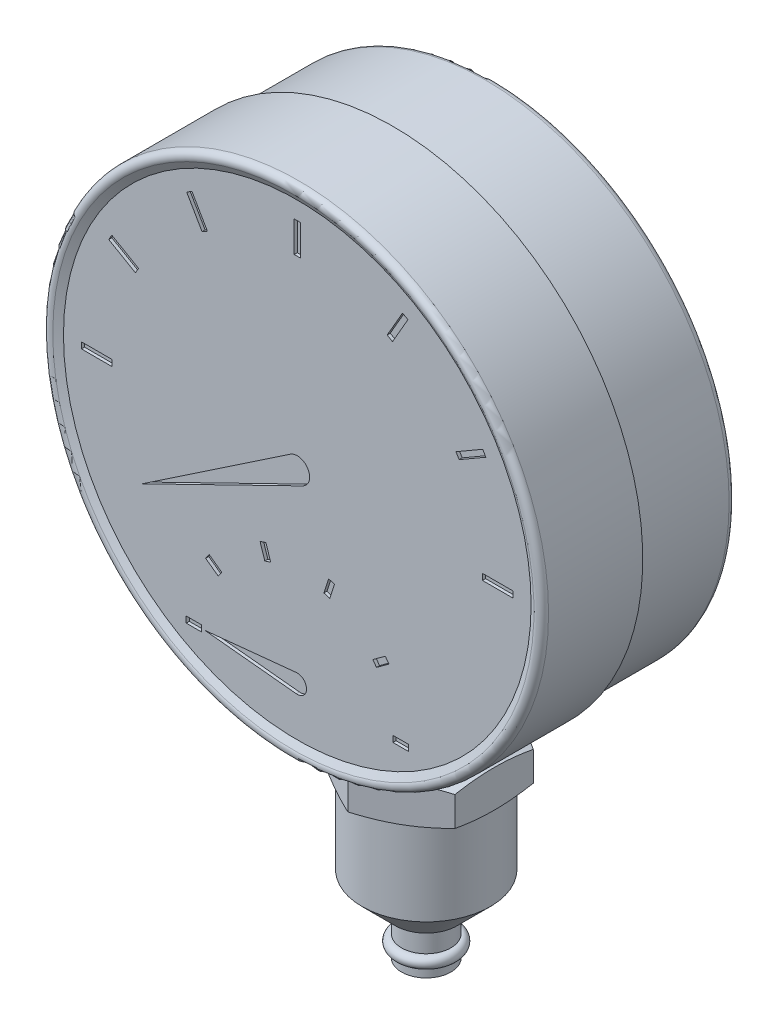
SolidWorks part; units mm, degrees
ref_plane "Horní" through (0, 0, 0) normal (0, 0, 1) x (1, 0, 0)
ref_plane "Přední" through (0, 0, 0) normal (0, 1, 0) x (1, 0, 0)
ref_plane "Pravá" through (0, 0, 0) normal (1, 0, 0) x (0, 0, -1)
sketch "Skica1" plane through (0, 0, 0) normal (1, 0, 0) x (0, 0, -1)
  line L0 (0, 40.5) -> (1.5, 37.9019)
  line L1 (0, 40.5) -> (17, 40.5)
  line L2 (1.5, 0) -> (33, 0)
  line L4 (33, 39.5) -> (33, 0)
  line L8 (0, 0) -> (-34.5616, 0) construction
  line L10 (1.5, 37.9019) -> (1.5, 0)
  line L12 (17, 40.5) -> (17, 39.5)
  line L13 (17, 39.5) -> (33, 39.5)
  dimension "D2" = 81
  dimension "D4" = 79
  dimension "D7" = 30
  dimension "D8" = 1.5
  dimension "D9" = 33
  dimension "D12" = 17
revolve "Rotovat1" add sketch "Skica1" angle 360 about L8
fillet "Zaoblit1" radius 1 2 edges at (-40.5, 0, 0) (-39.5, 0, -33)
sketch "Skica2" plane through (0, 0, -1.5) normal (0, 0, 1) x (1, 0, 0)
  line L0 (0, 35) -> (0, 0) construction
  line L3 (0.5, 30) -> (0.5, 35)
  line L4 (0.5, 30) -> (-0.5, 30)
  line L5 (0.5, 35) -> (-0.5, 35)
  line L6 (-0.5, 30) -> (-0.5, 35)
  dimension "D1" = 30
  dimension "D2" = 1
  dimension "D3" = 5
extrude "Odebrat vysunutím1" cut sketch "Skica2" against normal blind 0.5
pattern_circular "Kruhové pole1" count 12 over 360 about axis through (0, 0, 0) along (0, 0, 1) skipping 4, 5, 6, 7, 8 of "Odebrat vysunutím1"
sketch "Skica3" plane through (0, 0, -1.5) normal (0, 0, 1) x (1, 0, 0)
  line L0 (-1.1171, 1.659) -> (-25.1147, -14.5)
  line L1 (-25.1147, -14.5) -> (0.8782, -1.7969)
  line L2 (0, 0) -> (-25.1147, -14.5) construction
  line L4 (26.2308, 14.567) -> (30.5609, 17.067) construction
  line L5 (-0.15, -28.5075) -> (-15, -30)
  line L6 (-15, -30) -> (-0.15, -31.4925)
  line L7 (0, -30) -> (-15, -30) construction
  arc A0 (0.8782, -1.7969) -> (-1.1171, 1.659) centre (0, 0) ccw
  arc A1 (-0.15, -31.4925) -> (-0.15, -28.5075) centre (0, -30) ccw
  dimension "D1" = 2
  dimension "D4" = 1.5
  dimension "D2" = 29
  dimension "D3" = 30
  dimension "D5" = 15
extrude "Odebrat vysunutím2" cut sketch "Skica3" against normal blind 0.5
sketch "Skica8" plane through (0, 0, -1.5) normal (0, 0, 1) x (1, 0, 0)
  line L0 (-18, -30) -> (0, -30) construction
  line L1 (-15.5, -29.5) -> (-18, -29.5)
  line L2 (-15.5, -29.5) -> (-15.5, -30.5)
  line L3 (-15.5, -30.5) -> (-18, -30.5)
  line L4 (-18, -29.5) -> (-18, -30.5)
  line L5 (35, -0.5) -> (35, 0.5) construction
  dimension "D1" = 2.5
  dimension "D2" = 18
extrude "Odebrat vysunutím5" cut sketch "Skica8" against normal blind 0.5
pattern_circular "Kruhové pole2" count 6 every 36 about axis through (0, -30, 0) along (0, 0, 1) of "Odebrat vysunutím5"
ref_plane "Rovina2" through (0, -39.5, 0) normal (0, 1, 0) x (1, 0, 0)
sketch "Skica9" plane through (0, -39.5, 0) normal (0, 1, 0) x (1, 0, 0)
  line L0 (0, 15.4) -> (0, 0) construction
  line L1 (-7, 29.4) -> (7, 29.4)
  line L2 (-7, 29.4) -> (-7, 15.4)
  line L3 (-7, 15.4) -> (7, 15.4)
  line L4 (7, 29.4) -> (7, 15.4)
  line L5 (38.5, 33) -> (-38.5, 33) construction
  dimension "D1" = 14
  dimension "D2" = 3.6
extrude "Přidat vysunutím1" add sketch "Skica9" against normal blind 7 separate body
sketch "Skica10" plane through (0, 0, 0) normal (1, 0, 0) x (0, 0, -1)
  line L0 (22.4, -46.5) -> (22.4, -107.9209) construction
  line L1 (15.4, -46.5) -> (29.4, -46.5) construction
  line L2 (22.4, -46.5) -> (32.8, -46.5)
  line L3 (32.8, -46.5) -> (41.6469, -49.72)
  line L4 (41.6469, -49.72) -> (32.8, -52.94)
  line L6 (32.8, -52.94) -> (32.8, -66.54)
  line L7 (32.8, -66.54) -> (27.4, -71.94)
  line L8 (27.4, -71.94) -> (26.4, -71.94)
  line L9 (26.4, -71.94) -> (26.4, -75.54)
  line L10 (26.4, -75.54) -> (25.5, -75.54)
  line L11 (25.5, -75.54) -> (25.5, -77.54)
  line L12 (25.5, -77.54) -> (26.4, -77.54)
  line L13 (26.4, -77.54) -> (26.4, -78.94)
  line L14 (26.4, -78.94) -> (22.4, -78.94)
  line L15 (22.4, -78.94) -> (22.4, -46.5)
  line L16 (32.8, -46.5) -> (32.8, -52.94) construction
  line L17 (32.8, -49.72) -> (41.6469, -49.72) construction
  dimension "D1" = 20
  dimension "D2" = 6.44
  dimension "D3" = 20.8
  dimension "D4" = 25.44
  dimension "D5" = 7
  dimension "D6" = 45
  dimension "D7" = 13.6
  dimension "D8" = 8
  dimension "D9" = 1.4
  dimension "D10" = 0.9
  dimension "D11" = 2
revolve "Rotovat3" add sketch "Skica10" angle 360 about L0
sketch "Skica11" plane through (0, -78.94, 0) normal (0, -1, 0) x (1, 0, 0)
  line L1 (11, -16.0491) -> (0, -9.6983)
  line L2 (0, -9.6983) -> (-11, -16.0491)
  line L3 (-11, -16.0491) -> (-11, -28.7509)
  line L4 (-11, -28.7509) -> (0, -35.1017)
  line L5 (0, -35.1017) -> (11, -28.7509)
  line L6 (11, -28.7509) -> (11, -16.0491)
  circle A0 centre (0, -22.4) radius 11 construction
  dimension "D1" = 22
extrude "Odebrat vysunutím6" cut sketch "Skica11" against normal up to next (39.44 mm away) flip side to cut
sketch "Skica12" plane through (0, 0, 0) normal (1, 0, 0) x (0, 0, -1)
  line L0 (25.5, -76.54) -> (26.5, -76.54) construction
  line L1 (25.5, -77.54) -> (25.5, -75.54) construction
  line L2 (22.4, -75.54) -> (22.4, -83.9766) construction
  line L3 (19.3, -75.54) -> (25.5, -75.54) construction
  circle A0 centre (26.5, -76.54) radius 0.9
  dimension "D2" = 1.8
  dimension "D1" = 1
revolve "Rotovat4" add sketch "Skica12" angle 360 about L2
